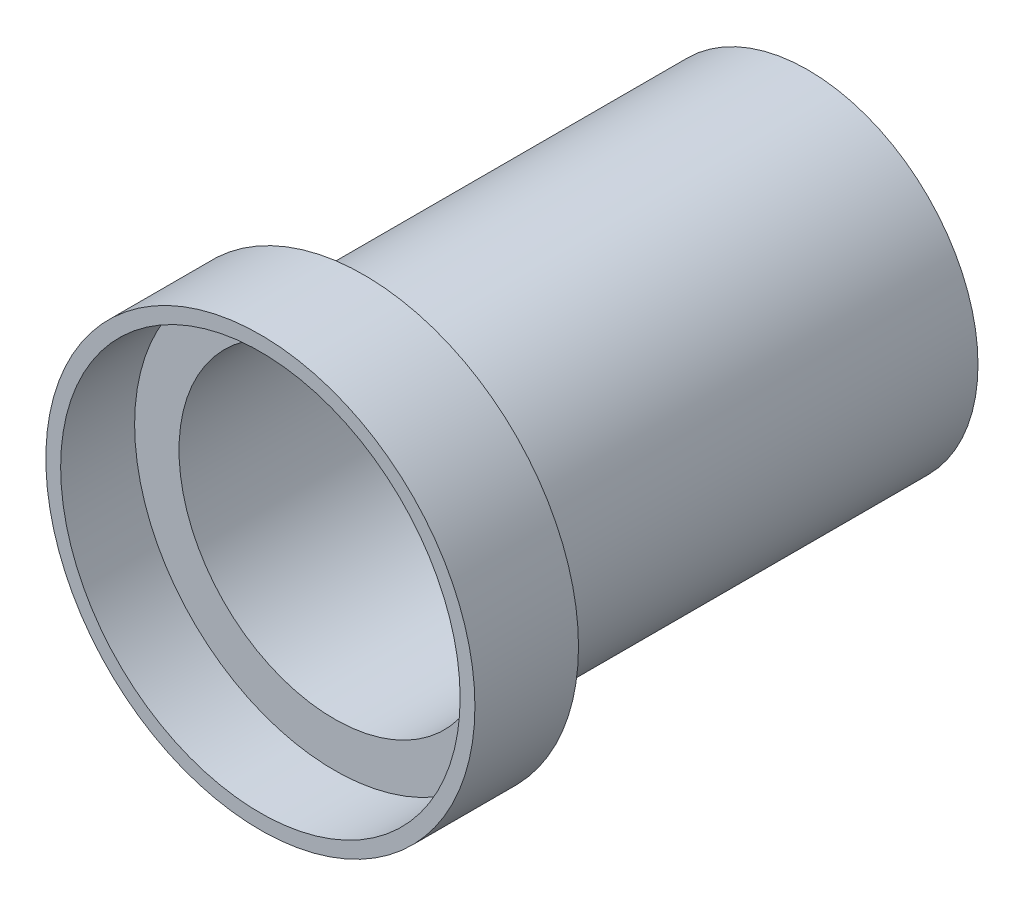
SolidWorks part; units mm, degrees
ref_plane "正面" through (0, 0, 0) normal (0, 0, 1) x (1, 0, 0)
ref_plane "平面" through (0, 0, 0) normal (0, 1, 0) x (1, 0, 0)
ref_plane "右側面" through (0, 0, 0) normal (1, 0, 0) x (0, 0, -1)
sketch "ｽｹｯﾁ1" plane through (0, 0, 0) normal (0, 0, 1) x (1, 0, 0)
  circle A0 centre (0, 0) radius 11.5
  dimension "D1" = 23
extrude "ﾎﾞｽ - 押し出し1" add sketch "ｽｹｯﾁ1" along normal blind 30
sketch "ｽｹｯﾁ3" plane through (0, 0, 30) normal (0, 0, 1) x (1, 0, 0)
  circle A0 centre (0, 0) radius 14.5
  dimension "D1" = 29
extrude "ﾎﾞｽ - 押し出し2" add sketch "ｽｹｯﾁ3" along normal blind 7
sketch "ｽｹｯﾁ4" plane through (0, 0, 37) normal (0, 0, 1) x (1, 0, 0)
  circle A0 centre (0, 0) radius 13.5
  dimension "D1" = 27
extrude "ｶｯﾄ - 押し出し3" cut sketch "ｽｹｯﾁ4" against normal blind 5
sketch "ｽｹｯﾁ2" plane through (0, 0, 0) normal (0, 0, 1) x (1, 0, 0)
  circle A0 centre (0, 0) radius 10.5
  dimension "D1" = 21
extrude "ｶｯﾄ - 押し出し2" cut sketch "ｽｹｯﾁ2" along normal through all from offset 1
